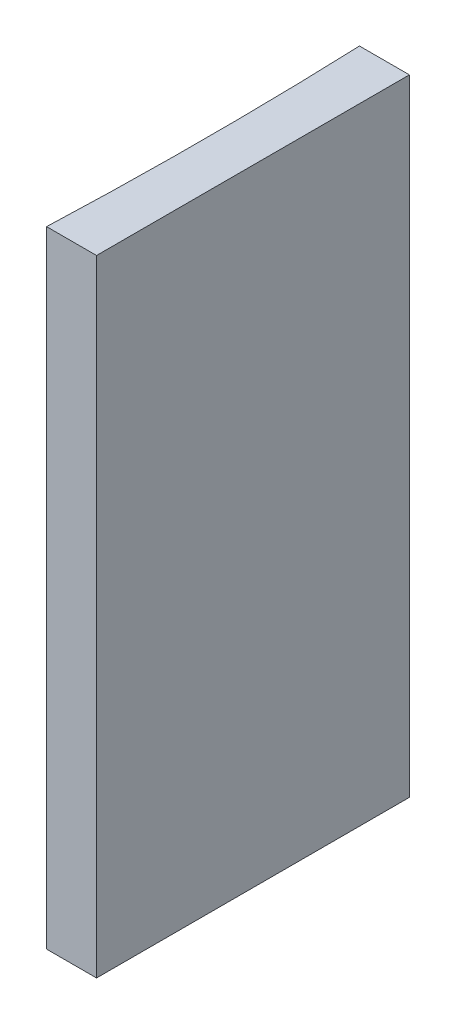
SolidWorks part; units mm, degrees
ref_plane "前视基准面" through (0, 0, 0) normal (0, 0, 1) x (1, 0, 0)
ref_plane "上视基准面" through (0, 0, 0) normal (0, 1, 0) x (1, 0, 0)
ref_plane "右视基准面" through (0, 0, 0) normal (1, 0, 0) x (0, 0, -1)
sketch "草图1" plane through (0, 0, 0) normal (0, 1, 0) x (1, 0, 0)
  line L0 (0, 0) -> (0, -20)
  line L1 (0, 0) -> (-3.1935, 0)
  line L2 (0, -20) -> (-3.1935, -20)
  line L3 (8.2336, -10) -> (-10.4405, -10) construction
  arc A0 (-3.1935, -20) -> (-3.1935, 0) centre (-261.5, -10) ccw
  point P7 (-3, -10)
  point P8 (0, -10)
  dimension "D2" = 258.5
  dimension "D3" = 3
  dimension "D1" = 20
extrude "凸台-拉伸1" add sketch "草图1" along normal blind 40
